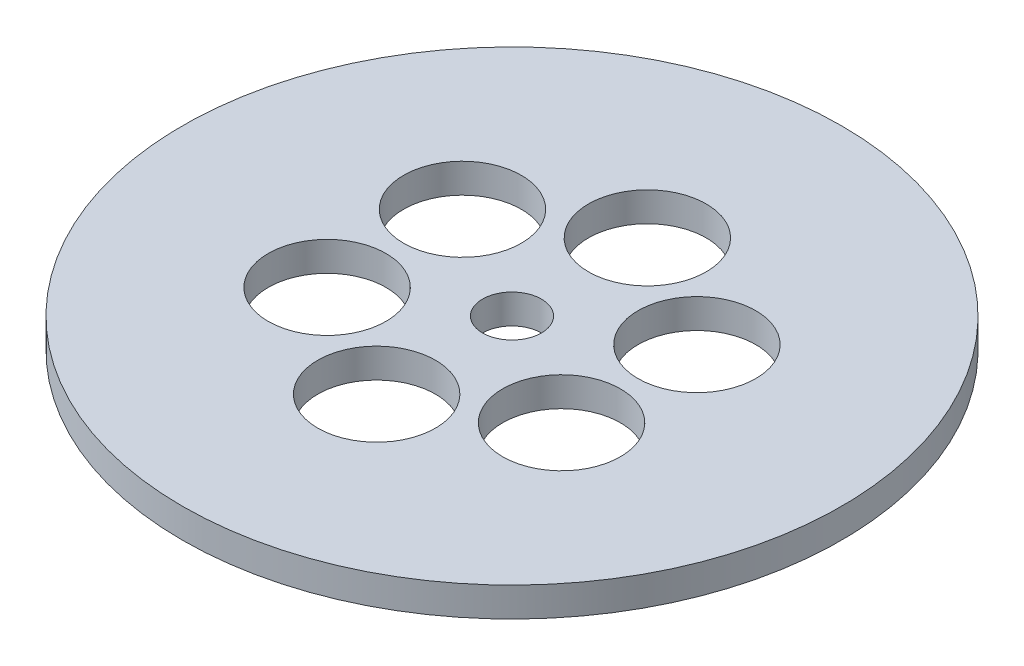
SolidWorks part; units mm, degrees
material "AISI 1020"
ref_plane "Front Plane" through (0, 0, 0) normal (0, 0, 1) x (1, 0, 0)
ref_plane "Top Plane" through (0, 0, 0) normal (0, 1, 0) x (1, 0, 0)
ref_plane "Right Plane" through (0, 0, 0) normal (1, 0, 0) x (0, 0, -1)
sketch "Sketch1" plane through (0, 0, 0) normal (0, 1, 0) x (1, 0, 0)
  circle A0 centre (0, 0) radius 71.12
  circle A1 centre (0, 0) radius 6.35
  circle A2 centre (0, 29.21) radius 12.7041
  circle A3 centre (25.2966, 14.605) radius 12.7041
  circle A4 centre (25.2966, -14.605) radius 12.7041
  circle A5 centre (0, -29.21) radius 12.7041
  circle A6 centre (-25.2966, -14.605) radius 12.7041
  circle A7 centre (-25.2966, 14.605) radius 12.7041
  point P6 (0, 0)
  point P18 (0, 0)
  dimension "D1" = 6
extrude "Boss-Extrude1" add sketch "Sketch1" along normal mid plane 6.35 contours A0 A7 A6 A5 A4 A3 A2 A1
